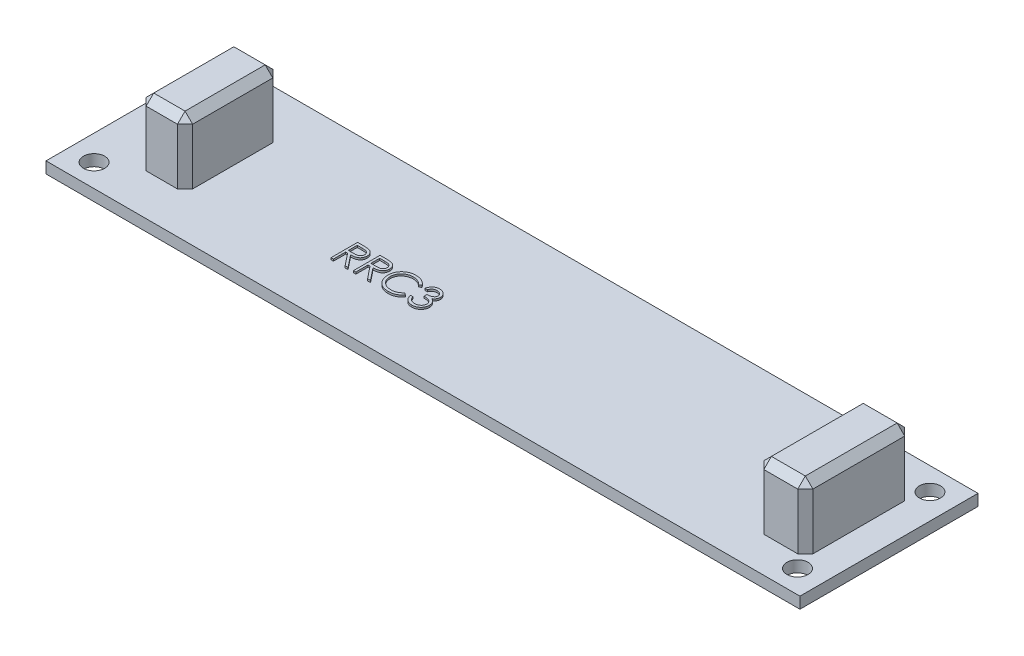
SolidWorks part; units mm, degrees
ref_plane "Front Plane" through (0, 0, 0) normal (0, 0, 1) x (1, 0, 0)
ref_plane "Top Plane" through (0, 0, 0) normal (0, 1, 0) x (1, 0, 0)
ref_plane "Right Plane" through (0, 0, 0) normal (1, 0, 0) x (0, 0, -1)
sketch "Sketch1" plane through (0, 0, 0) normal (0, 1, 0) x (1, 0, 0)
  line L0 (49.75, 23.5) -> (49.75, 0) construction
  line L1 (0, 0) -> (99.5, 0)
  line L2 (0, 0) -> (0, 23.5)
  line L3 (0, 23.5) -> (99.5, 23.5)
  line L4 (99.5, 0) -> (99.5, 23.5)
  line L5 (0, 11.75) -> (99.5, 11.75) construction
  circle A0 centre (3.33, 20.49) radius 1.397
  circle A1 centre (96.17, 20.49) radius 1.397
  circle A2 centre (96.17, 3.01) radius 1.397
  circle A3 centre (3.33, 3.01) radius 1.397
  dimension "D3" = 2.794
  dimension "D1" = 23.5
  dimension "D2" = 99.5
  dimension "D4" = 92.84
  dimension "D5" = 17.48
extrude "Boss-Extrude1" add sketch "Sketch1" along normal blind 1.5
sketch "Sketch2" plane through (0, 1.5, 0) normal (0, 1, 0) x (1, 0, 0)
  line L0 (89.0439, 18.8094) -> (95.5221, 18.8094)
  line L1 (6.7536, 18.0372) -> (12.8893, 18.0372)
  line L2 (6.7536, 18.0372) -> (6.7536, 5.4628)
  line L3 (6.7536, 5.4628) -> (12.8893, 5.4628)
  line L4 (12.8893, 18.0372) -> (12.8893, 5.4628)
  line L5 (6.7536, 18.0372) -> (12.8893, 5.4628) construction
  line L6 (6.7536, 5.4628) -> (12.8893, 18.0372) construction
  line L7 (89.0439, 18.8094) -> (89.0439, 4.6906)
  line L8 (89.0439, 4.6906) -> (95.5221, 4.6906)
  line L9 (95.5221, 18.8094) -> (95.5221, 4.6906)
  line L10 (89.0439, 18.8094) -> (95.5221, 4.6906) construction
  line L11 (89.0439, 4.6906) -> (95.5221, 18.8094) construction
  line L12 (0, 23.5) -> (0, 0) construction
  point P0 (9.8214, 11.75)
  point P5 (92.283, 11.75)
  point P12 (0, 0)
  point P13 (0, 11.75)
  point P14 (0, 0)
  dimension "D1" = 12.5744
  dimension "D2" = 6.1357
  dimension "D3" = 6.7536
extrude "Boss-Extrude2" add sketch "Sketch2" along normal blind 8.4
chamfer "Chamfer1" distance 1 angle 45 16 edges at (92.283, 9.9, -4.6906) (89.0439, 5.7, -4.6906) (89.0439, 9.9, -11.75) (89.0439, 5.7, -18.8094) (92.283, 9.9, -18.8094) (95.5221, 5.7, -18.8094) (95.5221, 9.9, -11.75) (95.5221, 5.7, -4.6906) (9.8214, 9.9, -5.4628) (6.7536, 5.7, -5.4628) (6.7536, 9.9, -11.75) (6.7536, 5.7, -18.0372) (9.8214, 9.9, -18.0372) (12.8893, 5.7, -18.0372) (12.8893, 9.9, -11.75) (12.8893, 5.7, -5.4628)
sketch "Sketch3" plane through (0, 1.5, 0) normal (0, 1, 0) x (1, 0, 0)
  text T0 "RRC3"
extrude "Boss-Extrude3" add sketch "Sketch3" along normal blind 0.25
